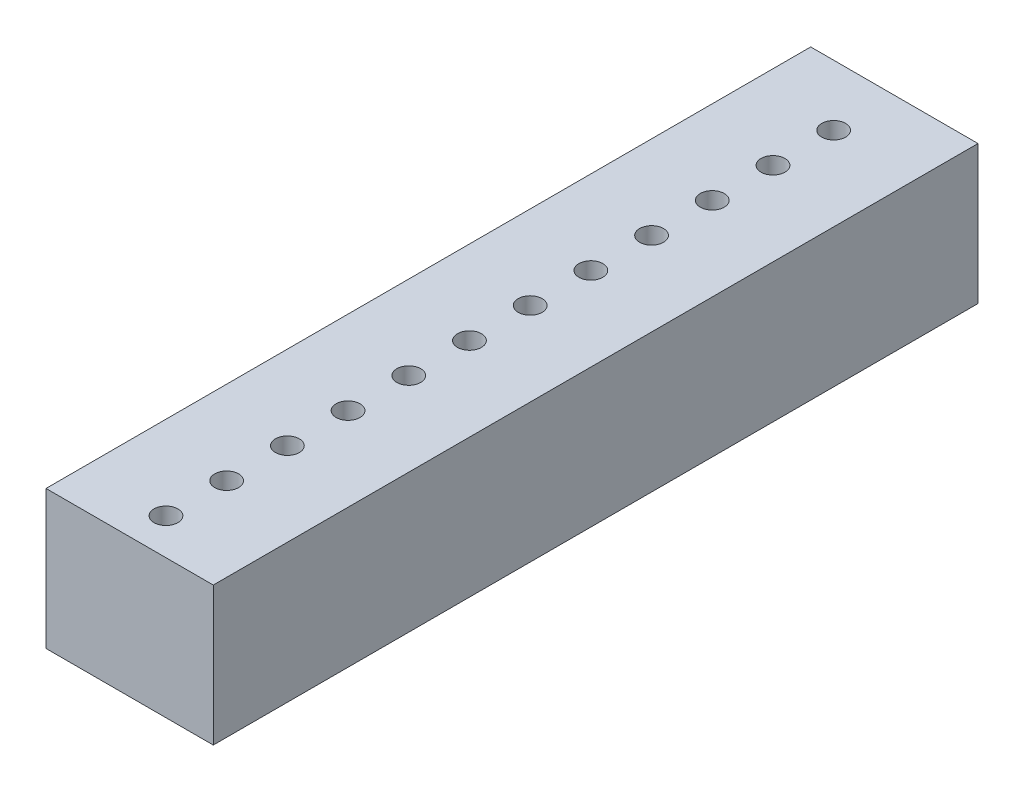
SolidWorks part; units mm, degrees
ref_plane "Front Plane" through (0, 0, 0) normal (0, 0, 1) x (1, 0, 0)
ref_plane "Top Plane" through (0, 0, 0) normal (0, 1, 0) x (1, 0, 0)
ref_plane "Right Plane" through (0, 0, 0) normal (1, 0, 0) x (0, 0, -1)
sketch "Sketch1" plane through (0, 0, 0) normal (0, 1, 0) x (1, 0, 0)
  line L1 (3.5, 16) -> (-3.5, 16)
  line L2 (3.5, 16) -> (3.5, -16)
  line L3 (3.5, -16) -> (-3.5, -16)
  line L4 (-3.5, 16) -> (-3.5, -16)
  line L5 (3.5, 16) -> (-3.5, -16) construction
  line L6 (3.5, -16) -> (-3.5, 16) construction
  line L7 (-0.96, 13.19) -> (1.58, 13.19) construction
  circle A0 centre (0, 13.19) radius 0.5
  circle A1 centre (1.58, 13.19) radius 0.5 construction
  point P0 (0, 0)
  point P13 (0, 16)
  dimension "D1" = 7
  dimension "D2" = 32
extrude "Boss-Extrude1" add sketch "Sketch1" along normal mid plane 5.8
sketch "Sketch2" plane through (0, 2.9, 0) normal (0, 1, 0) x (1, 0, 0)
  line L0 (3.5, 16) -> (-3.5, 16) construction
  circle A0 centre (0, 13.46) radius 0.5
  dimension "D1" = 1
  dimension "D2" = 2.54
extrude "Cut-Extrude1" cut sketch "Sketch2" against normal through all
pattern_linear "LPattern1" count 12 spacing 2.54 along (0, 0, 1) of "Cut-Extrude1"
